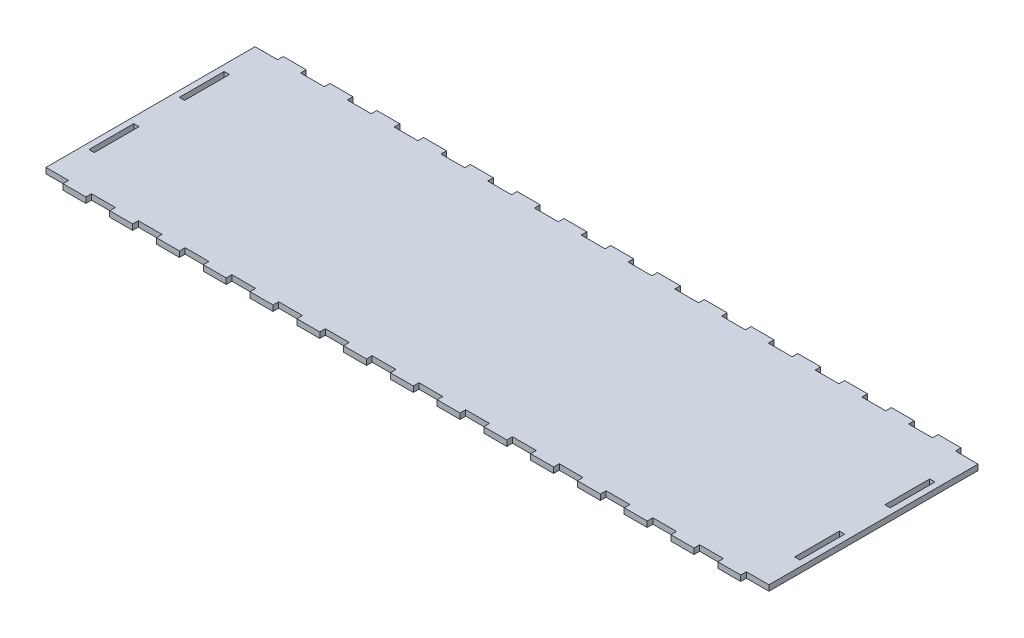
SolidWorks part; units mm, degrees
ref_plane "Front" through (0, 0, 0) normal (0, 0, 1) x (1, 0, 0)
ref_plane "Top" through (0, 0, 0) normal (0, 1, 0) x (1, 0, 0)
ref_plane "Right" through (0, 0, 0) normal (1, 0, 0) x (0, 0, -1)
sketch "Sketch1" plane through (0, 0, 0) normal (0, 1, 0) x (1, 0, 0)
  line L0 (196.85, -12.7) -> (196.85, -38.1) construction
  line L1 (200.025, -12.7) -> (196.85, -12.7) construction
  line L2 (200.025, -38.1) -> (200.025, -12.7) construction
  line L3 (196.85, -38.1) -> (200.025, -38.1) construction
  line L4 (196.85, 38.1) -> (196.85, 12.7) construction
  line L5 (200.025, 38.1) -> (196.85, 38.1) construction
  line L6 (200.025, 12.7) -> (200.025, 38.1) construction
  line L7 (196.85, 12.7) -> (200.025, 12.7) construction
  line L8 (-196.85, -38.1) -> (-196.85, -12.7) construction
  line L9 (-200.025, -38.1) -> (-196.85, -38.1) construction
  line L10 (-200.025, -12.7) -> (-200.025, -38.1) construction
  line L11 (-196.85, -12.7) -> (-200.025, -12.7) construction
  line L12 (-196.85, 12.7) -> (-196.85, 38.1) construction
  line L13 (-200.025, 12.7) -> (-196.85, 12.7) construction
  line L14 (-200.025, 38.1) -> (-200.025, 12.7) construction
  line L15 (-196.85, 38.1) -> (-200.025, 38.1) construction
  line L16 (-137.8857, 58.6835) -> (-137.9857, 58.6835) construction
  line L17 (-137.9857, 58.6835) -> (-151.3929, 58.6835) construction
  line L18 (-151.3929, 58.6835) -> (-151.4929, 58.6835) construction
  line L19 (-151.4929, 58.6835) -> (-151.4929, 61.8585) construction
  line L20 (-151.4929, 61.8585) -> (-164.1929, 61.8585) construction
  line L21 (-164.1929, 61.8585) -> (-164.1929, 58.6835) construction
  line L22 (-164.1929, 58.6835) -> (-164.2929, 58.6835) construction
  line L23 (-164.2929, 58.6835) -> (-177.7, 58.6835) construction
  line L24 (-177.7, 58.6835) -> (-177.8, 58.6835) construction
  line L25 (-177.8, 58.6835) -> (-177.8, 61.8585) construction
  line L26 (-177.8, 61.8585) -> (-190.5, 61.8585) construction
  line L27 (-190.5, 61.8585) -> (-190.5, 58.6835) construction
  line L28 (-190.5, 58.6835) -> (-190.6, 58.6835) construction
  line L29 (-190.6, 58.6835) -> (-203.2, 58.6835) construction
  line L30 (-203.2, 58.6835) -> (-203.2, -58.6835) construction
  line L31 (-203.2, -58.6835) -> (-190.6, -58.6835) construction
  line L32 (-190.6, -58.6835) -> (-190.5, -58.6835) construction
  line L33 (-190.5, -58.6835) -> (-190.5, -61.8585) construction
  line L34 (-190.5, -61.8585) -> (-177.8, -61.8585) construction
  line L35 (-177.8, -61.8585) -> (-177.8, -58.6835) construction
  line L36 (-177.8, -58.6835) -> (-177.7, -58.6835) construction
  line L37 (-177.7, -58.6835) -> (-164.2929, -58.6835) construction
  line L38 (-164.2929, -58.6835) -> (-164.1929, -58.6835) construction
  line L39 (-164.1929, -58.6835) -> (-164.1929, -61.8585) construction
  line L40 (-164.1929, -61.8585) -> (-151.4929, -61.8585) construction
  line L41 (-151.4929, -61.8585) -> (-151.4929, -58.6835) construction
  line L42 (-151.4929, -58.6835) -> (-151.3929, -58.6835) construction
  line L43 (-151.3929, -58.6835) -> (-137.9857, -58.6835) construction
  line L44 (-137.9857, -58.6835) -> (-137.8857, -58.6835) construction
  line L45 (-137.8857, -58.6835) -> (-137.8857, -61.8585) construction
  line L46 (-137.8857, -61.8585) -> (-125.1857, -61.8585) construction
  line L47 (-125.1857, -61.8585) -> (-125.1857, -58.6835) construction
  line L48 (-125.1857, -58.6835) -> (-125.0857, -58.6835) construction
  line L49 (-125.0857, -58.6835) -> (-111.6786, -58.6835) construction
  line L50 (-111.6786, -58.6835) -> (-111.5786, -58.6835) construction
  line L51 (-111.5786, -58.6835) -> (-111.5786, -61.8585) construction
  line L52 (-111.5786, -61.8585) -> (-98.8786, -61.8585) construction
  line L53 (-98.8786, -61.8585) -> (-98.8786, -58.6835) construction
  line L54 (-98.8786, -58.6835) -> (-98.7786, -58.6835) construction
  line L55 (-98.7786, -58.6835) -> (-85.3714, -58.6835) construction
  line L56 (-85.3714, -58.6835) -> (-85.2714, -58.6835) construction
  line L57 (-85.2714, -58.6835) -> (-85.2714, -61.8585) construction
  line L58 (-85.2714, -61.8585) -> (-72.5714, -61.8585) construction
  line L59 (-72.5714, -61.8585) -> (-72.5714, -58.6835) construction
  line L60 (-72.5714, -58.6835) -> (-72.4714, -58.6835) construction
  line L61 (-72.4714, -58.6835) -> (-59.0643, -58.6835) construction
  line L62 (-59.0643, -58.6835) -> (-58.9643, -58.6835) construction
  line L63 (-58.9643, -58.6835) -> (-58.9643, -61.8585) construction
  line L64 (-58.9643, -61.8585) -> (-46.2643, -61.8585) construction
  line L65 (-46.2643, -61.8585) -> (-46.2643, -58.6835) construction
  line L66 (-46.2643, -58.6835) -> (-46.1643, -58.6835) construction
  line L67 (-46.1643, -58.6835) -> (-32.7571, -58.6835) construction
  line L68 (-32.7571, -58.6835) -> (-32.6571, -58.6835) construction
  line L69 (-32.6571, -58.6835) -> (-32.6571, -61.8585) construction
  line L70 (-32.6571, -61.8585) -> (-19.9571, -61.8585) construction
  line L71 (-19.9571, -61.8585) -> (-19.9571, -58.6835) construction
  line L72 (-19.9571, -58.6835) -> (-19.8571, -58.6835) construction
  line L73 (-19.8571, -58.6835) -> (-6.45, -58.6835) construction
  line L74 (-6.45, -58.6835) -> (-6.35, -58.6835) construction
  line L75 (-6.35, -58.6835) -> (-6.35, -61.8585) construction
  line L76 (-6.35, -61.8585) -> (6.35, -61.8585) construction
  line L77 (6.35, -61.8585) -> (6.35, -58.6835) construction
  line L78 (6.35, -58.6835) -> (6.45, -58.6835) construction
  line L79 (6.45, -58.6835) -> (19.8571, -58.6835) construction
  line L80 (19.8571, -58.6835) -> (19.9571, -58.6835) construction
  line L81 (19.9571, -58.6835) -> (19.9571, -61.8585) construction
  line L82 (19.9571, -61.8585) -> (32.6571, -61.8585) construction
  line L83 (32.6571, -61.8585) -> (32.6571, -58.6835) construction
  line L84 (32.6571, -58.6835) -> (32.7571, -58.6835) construction
  line L85 (32.7571, -58.6835) -> (46.1643, -58.6835) construction
  line L86 (46.1643, -58.6835) -> (46.2643, -58.6835) construction
  line L87 (46.2643, -58.6835) -> (46.2643, -61.8585) construction
  line L88 (46.2643, -61.8585) -> (58.9643, -61.8585) construction
  line L89 (58.9643, -61.8585) -> (58.9643, -58.6835) construction
  line L90 (58.9643, -58.6835) -> (59.0643, -58.6835) construction
  line L91 (59.0643, -58.6835) -> (72.4714, -58.6835) construction
  line L92 (72.4714, -58.6835) -> (72.5714, -58.6835) construction
  line L93 (72.5714, -58.6835) -> (72.5714, -61.8585) construction
  line L94 (72.5714, -61.8585) -> (85.2714, -61.8585) construction
  line L95 (85.2714, -61.8585) -> (85.2714, -58.6835) construction
  line L96 (85.2714, -58.6835) -> (85.3714, -58.6835) construction
  line L97 (85.3714, -58.6835) -> (98.7786, -58.6835) construction
  line L98 (98.7786, -58.6835) -> (98.8786, -58.6835) construction
  line L99 (98.8786, -58.6835) -> (98.8786, -61.8585) construction
  line L100 (98.8786, -61.8585) -> (111.5786, -61.8585) construction
  line L101 (111.5786, -61.8585) -> (111.5786, -58.6835) construction
  line L102 (111.5786, -58.6835) -> (111.6786, -58.6835) construction
  line L103 (111.6786, -58.6835) -> (125.0857, -58.6835) construction
  line L104 (125.0857, -58.6835) -> (125.1857, -58.6835) construction
  line L105 (125.1857, -58.6835) -> (125.1857, -61.8585) construction
  line L106 (125.1857, -61.8585) -> (137.8857, -61.8585) construction
  line L107 (137.8857, -61.8585) -> (137.8857, -58.6835) construction
  line L108 (137.8857, -58.6835) -> (137.9857, -58.6835) construction
  line L109 (137.9857, -58.6835) -> (151.3929, -58.6835) construction
  line L110 (151.3929, -58.6835) -> (151.4929, -58.6835) construction
  line L111 (151.4929, -58.6835) -> (151.4929, -61.8585) construction
  line L112 (151.4929, -61.8585) -> (164.1929, -61.8585) construction
  line L113 (164.1929, -61.8585) -> (164.1929, -58.6835) construction
  line L114 (164.1929, -58.6835) -> (164.2929, -58.6835) construction
  line L115 (164.2929, -58.6835) -> (177.7, -58.6835) construction
  line L116 (177.7, -58.6835) -> (177.8, -58.6835) construction
  line L117 (177.8, -58.6835) -> (177.8, -61.8585) construction
  line L118 (177.8, -61.8585) -> (190.5, -61.8585) construction
  line L119 (190.5, -61.8585) -> (190.5, -58.6835) construction
  line L120 (190.5, -58.6835) -> (190.6, -58.6835) construction
  line L121 (190.6, -58.6835) -> (203.2, -58.6835) construction
  line L122 (203.2, -58.6835) -> (203.2, 58.6835) construction
  line L123 (203.2, 58.6835) -> (190.6, 58.6835) construction
  line L124 (190.6, 58.6835) -> (190.5, 58.6835) construction
  line L125 (190.5, 58.6835) -> (190.5, 61.8585) construction
  line L126 (190.5, 61.8585) -> (177.8, 61.8585) construction
  line L127 (177.8, 61.8585) -> (177.8, 58.6835) construction
  line L128 (177.8, 58.6835) -> (177.7, 58.6835) construction
  line L129 (177.7, 58.6835) -> (164.2929, 58.6835) construction
  line L130 (164.2929, 58.6835) -> (164.1929, 58.6835) construction
  line L131 (164.1929, 58.6835) -> (164.1929, 61.8585) construction
  line L132 (164.1929, 61.8585) -> (151.4929, 61.8585) construction
  line L133 (151.4929, 61.8585) -> (151.4929, 58.6835) construction
  line L134 (151.4929, 58.6835) -> (151.3929, 58.6835) construction
  line L135 (151.3929, 58.6835) -> (137.9857, 58.6835) construction
  line L136 (137.9857, 58.6835) -> (137.8857, 58.6835) construction
  line L137 (137.8857, 58.6835) -> (137.8857, 61.8585) construction
  line L138 (137.8857, 61.8585) -> (125.1857, 61.8585) construction
  line L139 (125.1857, 61.8585) -> (125.1857, 58.6835) construction
  line L140 (125.1857, 58.6835) -> (125.0857, 58.6835) construction
  line L141 (125.0857, 58.6835) -> (111.6786, 58.6835) construction
  line L142 (111.6786, 58.6835) -> (111.5786, 58.6835) construction
  line L143 (111.5786, 58.6835) -> (111.5786, 61.8585) construction
  line L144 (111.5786, 61.8585) -> (98.8786, 61.8585) construction
  line L145 (98.8786, 61.8585) -> (98.8786, 58.6835) construction
  line L146 (98.8786, 58.6835) -> (98.7786, 58.6835) construction
  line L147 (98.7786, 58.6835) -> (85.3714, 58.6835) construction
  line L148 (85.3714, 58.6835) -> (85.2714, 58.6835) construction
  line L149 (85.2714, 58.6835) -> (85.2714, 61.8585) construction
  line L150 (85.2714, 61.8585) -> (72.5714, 61.8585) construction
  line L151 (72.5714, 61.8585) -> (72.5714, 58.6835) construction
  line L152 (72.5714, 58.6835) -> (72.4714, 58.6835) construction
  line L153 (72.4714, 58.6835) -> (59.0643, 58.6835) construction
  line L154 (59.0643, 58.6835) -> (58.9643, 58.6835) construction
  line L155 (58.9643, 58.6835) -> (58.9643, 61.8585) construction
  line L156 (58.9643, 61.8585) -> (46.2643, 61.8585) construction
  line L157 (46.2643, 61.8585) -> (46.2643, 58.6835) construction
  line L158 (46.2643, 58.6835) -> (46.1643, 58.6835) construction
  line L159 (46.1643, 58.6835) -> (32.7571, 58.6835) construction
  line L160 (32.7571, 58.6835) -> (32.6571, 58.6835) construction
  line L161 (32.6571, 58.6835) -> (32.6571, 61.8585) construction
  line L162 (32.6571, 61.8585) -> (19.9571, 61.8585) construction
  line L163 (19.9571, 61.8585) -> (19.9571, 58.6835) construction
  line L164 (19.9571, 58.6835) -> (19.8571, 58.6835) construction
  line L165 (19.8571, 58.6835) -> (6.45, 58.6835) construction
  line L166 (6.45, 58.6835) -> (6.35, 58.6835) construction
  line L167 (6.35, 58.6835) -> (6.35, 61.8585) construction
  line L168 (6.35, 61.8585) -> (-6.35, 61.8585) construction
  line L169 (-6.35, 61.8585) -> (-6.35, 58.6835) construction
  line L170 (-6.35, 58.6835) -> (-6.45, 58.6835) construction
  line L171 (-6.45, 58.6835) -> (-19.8571, 58.6835) construction
  line L172 (-19.8571, 58.6835) -> (-19.9571, 58.6835) construction
  line L173 (-19.9571, 58.6835) -> (-19.9571, 61.8585) construction
  line L174 (-19.9571, 61.8585) -> (-32.6571, 61.8585) construction
  line L175 (-32.6571, 61.8585) -> (-32.6571, 58.6835) construction
  line L176 (-32.6571, 58.6835) -> (-32.7571, 58.6835) construction
  line L177 (-32.7571, 58.6835) -> (-46.1643, 58.6835) construction
  line L178 (-46.1643, 58.6835) -> (-46.2643, 58.6835) construction
  line L179 (-46.2643, 58.6835) -> (-46.2643, 61.8585) construction
  line L180 (-46.2643, 61.8585) -> (-58.9643, 61.8585) construction
  line L181 (-58.9643, 61.8585) -> (-58.9643, 58.6835) construction
  line L182 (-58.9643, 58.6835) -> (-59.0643, 58.6835) construction
  line L183 (-59.0643, 58.6835) -> (-72.4714, 58.6835) construction
  line L184 (-72.4714, 58.6835) -> (-72.5714, 58.6835) construction
  line L185 (-72.5714, 58.6835) -> (-72.5714, 61.8585) construction
  line L186 (-72.5714, 61.8585) -> (-85.2714, 61.8585) construction
  line L187 (-85.2714, 61.8585) -> (-85.2714, 58.6835) construction
  line L188 (-85.2714, 58.6835) -> (-85.3714, 58.6835) construction
  line L189 (-85.3714, 58.6835) -> (-98.7786, 58.6835) construction
  line L190 (-98.7786, 58.6835) -> (-98.8786, 58.6835) construction
  line L191 (-98.8786, 58.6835) -> (-98.8786, 61.8585) construction
  line L192 (-98.8786, 61.8585) -> (-111.5786, 61.8585) construction
  line L193 (-111.5786, 61.8585) -> (-111.5786, 58.6835) construction
  line L194 (-111.5786, 58.6835) -> (-111.6786, 58.6835) construction
  line L195 (-111.6786, 58.6835) -> (-125.0857, 58.6835) construction
  line L196 (-125.0857, 58.6835) -> (-125.1857, 58.6835) construction
  line L197 (-125.1857, 58.6835) -> (-125.1857, 61.8585) construction
  line L198 (-125.1857, 61.8585) -> (-137.8857, 61.8585) construction
  line L199 (-137.8857, 61.8585) -> (-137.8857, 58.6835) construction
  line L200 (-137.9873, 58.7851) -> (-137.9873, 58.7851)
  line L201 (-137.9873, 58.7851) -> (-151.3913, 58.7851)
  line L202 (-151.3913, 58.7851) -> (-151.3913, 58.7851)
  line L203 (-151.3913, 58.7851) -> (-151.3913, 61.9601)
  line L204 (-151.3913, 61.9601) -> (-164.2945, 61.9601)
  line L205 (-164.2945, 61.9601) -> (-164.2945, 58.7851)
  line L206 (-164.2945, 58.7851) -> (-164.2945, 58.7851)
  line L207 (-164.2945, 58.7851) -> (-177.6984, 58.7851)
  line L208 (-177.6984, 58.7851) -> (-177.6984, 58.7851)
  line L209 (-177.6984, 58.7851) -> (-177.6984, 61.9601)
  line L210 (-177.6984, 61.9601) -> (-190.6016, 61.9601)
  line L211 (-190.6016, 61.9601) -> (-190.6016, 58.7851)
  line L212 (-190.6016, 58.7851) -> (-190.6016, 58.7851)
  line L213 (-190.6016, 58.7851) -> (-203.3016, 58.7851)
  line L214 (-203.3016, 58.7851) -> (-203.3016, -58.7851)
  line L215 (-203.3016, -58.7851) -> (-190.6016, -58.7851)
  line L216 (-190.6016, -58.7851) -> (-190.6016, -58.7851)
  line L217 (-190.6016, -58.7851) -> (-190.6016, -61.9601)
  line L218 (-190.6016, -61.9601) -> (-177.6984, -61.9601)
  line L219 (-177.6984, -61.9601) -> (-177.6984, -58.7851)
  line L220 (-177.6984, -58.7851) -> (-177.6984, -58.7851)
  line L221 (-177.6984, -58.7851) -> (-164.2945, -58.7851)
  line L222 (-164.2945, -58.7851) -> (-164.2945, -58.7851)
  line L223 (-164.2945, -58.7851) -> (-164.2945, -61.9601)
  line L224 (-164.2945, -61.9601) -> (-151.3913, -61.9601)
  line L225 (-151.3913, -61.9601) -> (-151.3913, -58.7851)
  line L226 (-151.3913, -58.7851) -> (-151.3913, -58.7851)
  line L227 (-151.3913, -58.7851) -> (-137.9873, -58.7851)
  line L228 (-137.9873, -58.7851) -> (-137.9873, -58.7851)
  line L229 (-137.9873, -58.7851) -> (-137.9873, -61.9601)
  line L230 (-137.9873, -61.9601) -> (-125.0841, -61.9601)
  line L231 (-125.0841, -61.9601) -> (-125.0841, -58.7851)
  line L232 (-125.0841, -58.7851) -> (-125.0841, -58.7851)
  line L233 (-125.0841, -58.7851) -> (-111.6802, -58.7851)
  line L234 (-111.6802, -58.7851) -> (-111.6802, -58.7851)
  line L235 (-111.6802, -58.7851) -> (-111.6802, -61.9601)
  line L236 (-111.6802, -61.9601) -> (-98.777, -61.9601)
  line L237 (-98.777, -61.9601) -> (-98.777, -58.7851)
  line L238 (-98.777, -58.7851) -> (-98.777, -58.7851)
  line L239 (-98.777, -58.7851) -> (-85.373, -58.7851)
  line L240 (-85.373, -58.7851) -> (-85.373, -58.7851)
  line L241 (-85.373, -58.7851) -> (-85.373, -61.9601)
  line L242 (-85.373, -61.9601) -> (-72.4698, -61.9601)
  line L243 (-72.4698, -61.9601) -> (-72.4698, -58.7851)
  line L244 (-72.4698, -58.7851) -> (-72.4698, -58.7851)
  line L245 (-72.4698, -58.7851) -> (-59.0659, -58.7851)
  line L246 (-59.0659, -58.7851) -> (-59.0659, -58.7851)
  line L247 (-59.0659, -58.7851) -> (-59.0659, -61.9601)
  line L248 (-59.0659, -61.9601) -> (-46.1627, -61.9601)
  line L249 (-46.1627, -61.9601) -> (-46.1627, -58.7851)
  line L250 (-46.1627, -58.7851) -> (-46.1627, -58.7851)
  line L251 (-46.1627, -58.7851) -> (-32.7587, -58.7851)
  line L252 (-32.7587, -58.7851) -> (-32.7587, -58.7851)
  line L253 (-32.7587, -58.7851) -> (-32.7587, -61.9601)
  line L254 (-32.7587, -61.9601) -> (-19.8555, -61.9601)
  line L255 (-19.8555, -61.9601) -> (-19.8555, -58.7851)
  line L256 (-19.8555, -58.7851) -> (-19.8555, -58.7851)
  line L257 (-19.8555, -58.7851) -> (-6.4516, -58.7851)
  line L258 (-6.4516, -58.7851) -> (-6.4516, -58.7851)
  line L259 (-6.4516, -58.7851) -> (-6.4516, -61.9601)
  line L260 (-6.4516, -61.9601) -> (6.4516, -61.9601)
  line L261 (6.4516, -61.9601) -> (6.4516, -58.7851)
  line L262 (6.4516, -58.7851) -> (6.4516, -58.7851)
  line L263 (6.4516, -58.7851) -> (19.8555, -58.7851)
  line L264 (19.8555, -58.7851) -> (19.8555, -58.7851)
  line L265 (19.8555, -58.7851) -> (19.8555, -61.9601)
  line L266 (19.8555, -61.9601) -> (32.7587, -61.9601)
  line L267 (32.7587, -61.9601) -> (32.7587, -58.7851)
  line L268 (32.7587, -58.7851) -> (32.7587, -58.7851)
  line L269 (32.7587, -58.7851) -> (46.1627, -58.7851)
  line L270 (46.1627, -58.7851) -> (46.1627, -58.7851)
  line L271 (46.1627, -58.7851) -> (46.1627, -61.9601)
  line L272 (46.1627, -61.9601) -> (59.0659, -61.9601)
  line L273 (59.0659, -61.9601) -> (59.0659, -58.7851)
  line L274 (59.0659, -58.7851) -> (59.0659, -58.7851)
  line L275 (59.0659, -58.7851) -> (72.4698, -58.7851)
  line L276 (72.4698, -58.7851) -> (72.4698, -58.7851)
  line L277 (72.4698, -58.7851) -> (72.4698, -61.9601)
  line L278 (72.4698, -61.9601) -> (85.373, -61.9601)
  line L279 (85.373, -61.9601) -> (85.373, -58.7851)
  line L280 (85.373, -58.7851) -> (85.373, -58.7851)
  line L281 (85.373, -58.7851) -> (98.777, -58.7851)
  line L282 (98.777, -58.7851) -> (98.777, -58.7851)
  line L283 (98.777, -58.7851) -> (98.777, -61.9601)
  line L284 (98.777, -61.9601) -> (111.6802, -61.9601)
  line L285 (111.6802, -61.9601) -> (111.6802, -58.7851)
  line L286 (111.6802, -58.7851) -> (111.6802, -58.7851)
  line L287 (111.6802, -58.7851) -> (125.0841, -58.7851)
  line L288 (125.0841, -58.7851) -> (125.0841, -58.7851)
  line L289 (125.0841, -58.7851) -> (125.0841, -61.9601)
  line L290 (125.0841, -61.9601) -> (137.9873, -61.9601)
  line L291 (137.9873, -61.9601) -> (137.9873, -58.7851)
  line L292 (137.9873, -58.7851) -> (137.9873, -58.7851)
  line L293 (137.9873, -58.7851) -> (151.3913, -58.7851)
  line L294 (151.3913, -58.7851) -> (151.3913, -58.7851)
  line L295 (151.3913, -58.7851) -> (151.3913, -61.9601)
  line L296 (151.3913, -61.9601) -> (164.2945, -61.9601)
  line L297 (164.2945, -61.9601) -> (164.2945, -58.7851)
  line L298 (164.2945, -58.7851) -> (164.2945, -58.7851)
  line L299 (164.2945, -58.7851) -> (177.6984, -58.7851)
  line L300 (177.6984, -58.7851) -> (177.6984, -58.7851)
  line L301 (177.6984, -58.7851) -> (177.6984, -61.9601)
  line L302 (177.6984, -61.9601) -> (190.6016, -61.9601)
  line L303 (190.6016, -61.9601) -> (190.6016, -58.7851)
  line L304 (190.6016, -58.7851) -> (190.6016, -58.7851)
  line L305 (190.6016, -58.7851) -> (203.3016, -58.7851)
  line L306 (203.3016, -58.7851) -> (203.3016, 58.7851)
  line L307 (203.3016, 58.7851) -> (190.6016, 58.7851)
  line L308 (190.6016, 58.7851) -> (190.6016, 58.7851)
  line L309 (190.6016, 58.7851) -> (190.6016, 61.9601)
  line L310 (190.6016, 61.9601) -> (177.6984, 61.9601)
  line L311 (177.6984, 61.9601) -> (177.6984, 58.7851)
  line L312 (177.6984, 58.7851) -> (177.6984, 58.7851)
  line L313 (177.6984, 58.7851) -> (164.2945, 58.7851)
  line L314 (164.2945, 58.7851) -> (164.2945, 58.7851)
  line L315 (164.2945, 58.7851) -> (164.2945, 61.9601)
  line L316 (164.2945, 61.9601) -> (151.3913, 61.9601)
  line L317 (151.3913, 61.9601) -> (151.3913, 58.7851)
  line L318 (151.3913, 58.7851) -> (151.3913, 58.7851)
  line L319 (151.3913, 58.7851) -> (137.9873, 58.7851)
  line L320 (137.9873, 58.7851) -> (137.9873, 58.7851)
  line L321 (137.9873, 58.7851) -> (137.9873, 61.9601)
  line L322 (137.9873, 61.9601) -> (125.0841, 61.9601)
  line L323 (125.0841, 61.9601) -> (125.0841, 58.7851)
  line L324 (125.0841, 58.7851) -> (125.0841, 58.7851)
  line L325 (125.0841, 58.7851) -> (111.6802, 58.7851)
  line L326 (111.6802, 58.7851) -> (111.6802, 58.7851)
  line L327 (111.6802, 58.7851) -> (111.6802, 61.9601)
  line L328 (111.6802, 61.9601) -> (98.777, 61.9601)
  line L329 (98.777, 61.9601) -> (98.777, 58.7851)
  line L330 (98.777, 58.7851) -> (98.777, 58.7851)
  line L331 (98.777, 58.7851) -> (85.373, 58.7851)
  line L332 (85.373, 58.7851) -> (85.373, 58.7851)
  line L333 (85.373, 58.7851) -> (85.373, 61.9601)
  line L334 (85.373, 61.9601) -> (72.4698, 61.9601)
  line L335 (72.4698, 61.9601) -> (72.4698, 58.7851)
  line L336 (72.4698, 58.7851) -> (72.4698, 58.7851)
  line L337 (72.4698, 58.7851) -> (59.0659, 58.7851)
  line L338 (59.0659, 58.7851) -> (59.0659, 58.7851)
  line L339 (59.0659, 58.7851) -> (59.0659, 61.9601)
  line L340 (59.0659, 61.9601) -> (46.1627, 61.9601)
  line L341 (46.1627, 61.9601) -> (46.1627, 58.7851)
  line L342 (46.1627, 58.7851) -> (46.1627, 58.7851)
  line L343 (46.1627, 58.7851) -> (32.7587, 58.7851)
  line L344 (32.7587, 58.7851) -> (32.7587, 58.7851)
  line L345 (32.7587, 58.7851) -> (32.7587, 61.9601)
  line L346 (32.7587, 61.9601) -> (19.8555, 61.9601)
  line L347 (19.8555, 61.9601) -> (19.8555, 58.7851)
  line L348 (19.8555, 58.7851) -> (19.8555, 58.7851)
  line L349 (19.8555, 58.7851) -> (6.4516, 58.7851)
  line L350 (6.4516, 58.7851) -> (6.4516, 58.7851)
  line L351 (6.4516, 58.7851) -> (6.4516, 61.9601)
  line L352 (6.4516, 61.9601) -> (-6.4516, 61.9601)
  line L353 (-6.4516, 61.9601) -> (-6.4516, 58.7851)
  line L354 (-6.4516, 58.7851) -> (-6.4516, 58.7851)
  line L355 (-6.4516, 58.7851) -> (-19.8555, 58.7851)
  line L356 (-19.8555, 58.7851) -> (-19.8555, 58.7851)
  line L357 (-19.8555, 58.7851) -> (-19.8555, 61.9601)
  line L358 (-19.8555, 61.9601) -> (-32.7587, 61.9601)
  line L359 (-32.7587, 61.9601) -> (-32.7587, 58.7851)
  line L360 (-32.7587, 58.7851) -> (-32.7587, 58.7851)
  line L361 (-32.7587, 58.7851) -> (-46.1627, 58.7851)
  line L362 (-46.1627, 58.7851) -> (-46.1627, 58.7851)
  line L363 (-46.1627, 58.7851) -> (-46.1627, 61.9601)
  line L364 (-46.1627, 61.9601) -> (-59.0659, 61.9601)
  line L365 (-59.0659, 61.9601) -> (-59.0659, 58.7851)
  line L366 (-59.0659, 58.7851) -> (-59.0659, 58.7851)
  line L367 (-59.0659, 58.7851) -> (-72.4698, 58.7851)
  line L368 (-72.4698, 58.7851) -> (-72.4698, 58.7851)
  line L369 (-72.4698, 58.7851) -> (-72.4698, 61.9601)
  line L370 (-72.4698, 61.9601) -> (-85.373, 61.9601)
  line L371 (-85.373, 61.9601) -> (-85.373, 58.7851)
  line L372 (-85.373, 58.7851) -> (-85.373, 58.7851)
  line L373 (-85.373, 58.7851) -> (-98.777, 58.7851)
  line L374 (-98.777, 58.7851) -> (-98.777, 58.7851)
  line L375 (-98.777, 58.7851) -> (-98.777, 61.9601)
  line L376 (-98.777, 61.9601) -> (-111.6802, 61.9601)
  line L377 (-111.6802, 61.9601) -> (-111.6802, 58.7851)
  line L378 (-111.6802, 58.7851) -> (-111.6802, 58.7851)
  line L379 (-111.6802, 58.7851) -> (-125.0841, 58.7851)
  line L380 (-125.0841, 58.7851) -> (-125.0841, 58.7851)
  line L381 (-125.0841, 58.7851) -> (-125.0841, 61.9601)
  line L382 (-125.0841, 61.9601) -> (-137.9873, 61.9601)
  line L383 (-137.9873, 61.9601) -> (-137.9873, 58.7851)
  line L384 (-196.9516, 12.8016) -> (-196.9516, 37.9984)
  line L385 (-196.9516, 37.9984) -> (-199.9234, 37.9984)
  line L386 (-199.9234, 37.9984) -> (-199.9234, 12.8016)
  line L387 (-199.9234, 12.8016) -> (-196.9516, 12.8016)
  line L388 (-199.9234, -37.9984) -> (-196.9516, -37.9984)
  line L389 (-196.9516, -37.9984) -> (-196.9516, -12.8016)
  line L390 (-196.9516, -12.8016) -> (-199.9234, -12.8016)
  line L391 (-199.9234, -12.8016) -> (-199.9234, -37.9984)
  line L392 (196.9516, 12.8016) -> (199.9234, 12.8016)
  line L393 (199.9234, 12.8016) -> (199.9234, 37.9984)
  line L394 (199.9234, 37.9984) -> (196.9516, 37.9984)
  line L395 (196.9516, 37.9984) -> (196.9516, 12.8016)
  line L396 (196.9516, -37.9984) -> (199.9234, -37.9984)
  line L397 (199.9234, -37.9984) -> (199.9234, -12.8016)
  line L398 (199.9234, -12.8016) -> (196.9516, -12.8016)
  line L399 (196.9516, -12.8016) -> (196.9516, -37.9984)
  dimension "D1" = 0.1016
  dimension "D2" = 0.1016
  dimension "D3" = 0.1016
  dimension "D4" = 0.1016
  dimension "D5" = 0.1016
extrude "Boss-Extrude1" add sketch "Sketch1" along normal blind 3.175
